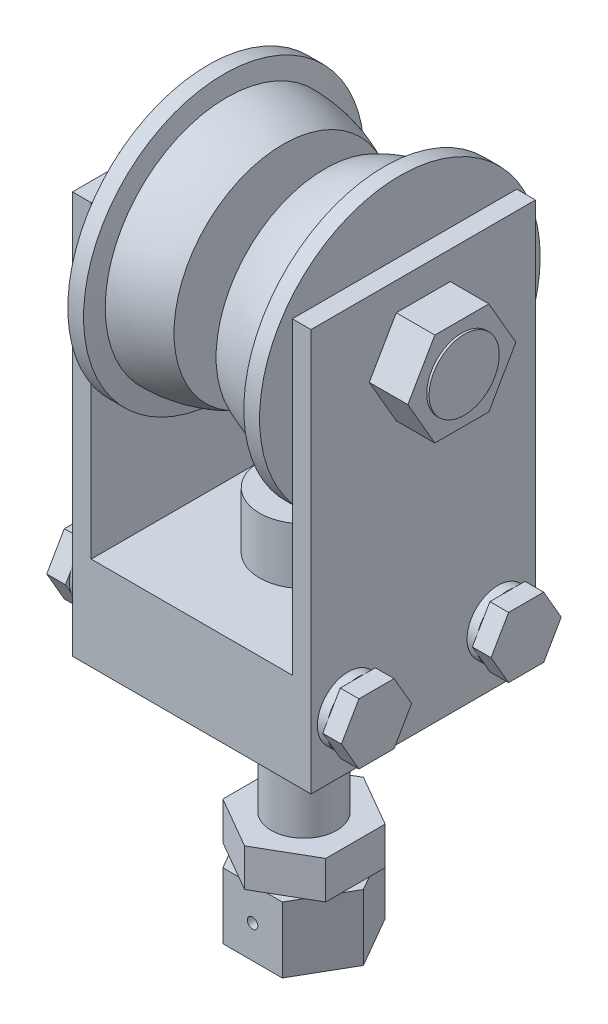
SolidWorks part; units mm, degrees
ref_plane "Front" through (0, 0, 0) normal (0, 0, 1) x (1, 0, 0)
ref_plane "Top" through (0, 0, 0) normal (0, 1, 0) x (1, 0, 0)
ref_plane "Right" through (0, 0, 0) normal (1, 0, 0) x (0, 0, -1)
ref_plane "Z PLANE" through (0, 0, 0) normal (0, 0, 1) x (1, 0, 0)
ref_plane "YOKE BOTTOM" through (0, 0, 0) normal (0, 1, 0) x (-1, 0, 0)
ref_plane "X PLANE" through (0, 0, 0) normal (1, 0, 0) x (0, 0, -1)
sketch "YOKE CROSS SECTION" plane through (0, 0, 0) normal (1, 0, 0) x (0, 0, -1)
  line L0 (0, 0) -> (0, 57.0916) construction
  line L1 (0, 84.8167) -> (0, -84.8167) construction
  line L2 (-76.2, 0) -> (76.2, 0)
  line L3 (69.1602, 0) -> (-69.1602, 0) construction
  line L4 (76.2, 0) -> (76.2, 63.5)
  line L5 (-76.2, 0) -> (-76.2, 63.5)
  line L6 (76.2, 63.5) -> (-76.2, 63.5)
  point P12 (0, 63.5)
  dimension "D1" = 63.5
  dimension "D2" = 152.4
ref_plane "1/2 YOKE LENGTH (A)" through (68.2625, 0, 0) normal (1, 0, 0) x (0, 0, -1)
extrude "YOKE" add sketch "YOKE CROSS SECTION" along normal up to surface (68.2625 mm away) up to plane "1/2 YOKE LENGTH (A)"
sketch "SIDEPLATE PROFILE" plane through (68.2625, 0, 0) normal (1, 0, 0) x (0, 0, -1)
  line L0 (0, 0) -> (0, 74.7424) construction
  line L1 (0, 84.8167) -> (0, -84.8167) construction
  line L2 (-76.2, 0) -> (76.2, 0)
  line L3 (76.2, 0) -> (76.2, 273.05)
  line L4 (-76.2, 0) -> (-76.2, 273.05)
  line L5 (76.2, 273.05) -> (-76.2, 273.05)
  point P11 (0, 273.05)
  dimension "D1" = 273.05
ref_plane "WHEEL HEIGHT" through (0, 222.25, 0) normal (0, 1, 0) x (-1, 0, 0)
ref_plane "SCREW LOCATION X" through (0, 0, 50.8) normal (0, 0, 1) x (1, 0, 0)
ref_plane "SCREW LOCATION Y" through (0, 38.1, 0) normal (0, 1, 0) x (-1, 0, 0)
extrude "SIDEPLATE" add sketch "SIDEPLATE PROFILE" along normal blind 12.7
sketch "WHEEL PIN NUT PROFILE" plane through (80.9625, 0, 0) normal (1, 0, 0) x (0, 0, -1)
  line L0 (0, 84.8167) -> (0, -84.8167) construction
  line L1 (36.6617, 222.25) -> (18.3309, 254)
  line L2 (18.3309, 254) -> (-18.3309, 254)
  line L3 (-18.3309, 254) -> (-36.6617, 222.25)
  line L4 (-36.6617, 222.25) -> (-18.3309, 190.5)
  line L5 (-18.3309, 190.5) -> (18.3309, 190.5)
  line L6 (18.3309, 190.5) -> (36.6617, 222.25)
  line L7 (69.1602, 222.25) -> (-69.1602, 222.25) construction
  circle A0 centre (0, 222.25) radius 31.75 construction
  dimension "D1" = 63.5
extrude "WHEEL PIN NUT" add sketch "WHEEL PIN NUT PROFILE" along normal blind 26.1937
sketch "WHEEL PIN PROJECTION PROFILE" plane through (107.1563, 0, 0) normal (1, 0, 0) x (0, 0, -1)
  line L0 (0, 84.8167) -> (0, -84.8167) construction
  line L1 (69.1602, 222.25) -> (-69.1602, 222.25) construction
  circle A0 centre (0, 222.25) radius 23.8125
  dimension "D1" = 47.625
extrude "WHEEL PIN PROJECTION" add sketch "WHEEL PIN PROJECTION PROFILE" along normal blind 1.5875
sketch "LOCKNUTS PROFILE" plane through (80.9625, 0, 0) normal (1, 0, 0) x (0, 0, -1)
  line L0 (-50.8, 84.8167) -> (-50.8, -84.8167) construction
  line L1 (50, 38.1) -> (-50, 38.1) construction
  circle A0 centre (-50.8, 38.1) radius 21.0947
  dimension "D1" = 42.1894
extrude "LOCKNUTS" add sketch "LOCKNUTS PROFILE" along normal blind 6.35
sketch "SCREWS PROFILE" plane through (87.3125, 0, 0) normal (1, 0, 0) x (0, 0, -1)
  line L0 (50, 38.1) -> (-50, 38.1) construction
  line L1 (-26.9699, 38.1) -> (-38.8849, 58.7375)
  line L2 (-38.8849, 58.7375) -> (-62.7151, 58.7375)
  line L3 (-62.7151, 58.7375) -> (-74.6301, 38.1)
  line L4 (-74.6301, 38.1) -> (-62.7151, 17.4625)
  line L5 (-62.7151, 17.4625) -> (-38.8849, 17.4625)
  line L6 (-38.8849, 17.4625) -> (-26.9699, 38.1)
  line L7 (-50.8, 84.8167) -> (-50.8, -84.8167) construction
  circle A0 centre (-50.8, 38.1) radius 20.6375 construction
  dimension "D1" = 41.275
extrude "SCREWS" add sketch "SCREWS PROFILE" along normal blind 12.7
sketch "PROFILE" plane through (0, 63.5, 0) normal (0, 1, 0) x (-1, 0, 0)
  line L0 (84.8167, 0) -> (-84.8167, 0) construction
  line L1 (0, 83.2389) -> (0, -83.2389) construction
  circle A0 centre (0, 0) radius 30.1625
  dimension "D1" = 60.325
extrude "KING BOLT HEAD" add sketch "PROFILE" along normal blind 38.1
mirror "Mirror1" about plane through (0, 0, 0) normal (0, 0, 1) of "SCREWS", "LOCKNUTS"
mirror "Mirror5" about plane through (0, 0, 0) normal (1, 0, 0) of bodies 112
ref_plane "TOP OF NUT" through (0, -88.9, 0) normal (0, 1, 0) x (-1, 0, 0)
sketch "DIA." plane through (0, 0, 0) normal (0, -1, 0) x (1, 0, 0)
  line L0 (84.8167, 0) -> (-84.8167, 0) construction
  line L1 (0, -83.2389) -> (0, 83.2389) construction
  circle A0 centre (0, 0) radius 22.225
  dimension "D1" = 44.45
extrude "KING BOLT" add sketch "DIA." along normal up to surface (88.9 mm away) up to plane "TOP OF NUT"
sketch "KING BOLT JAN NUT PROFILE" plane through (0, -88.9, 0) normal (0, -1, 0) x (1, 0, 0)
  line L0 (84.8167, 0) -> (-84.8167, 0) construction
  line L1 (0, -40.3279) -> (34.925, -20.164)
  line L2 (34.925, -20.164) -> (34.925, 20.164)
  line L3 (34.925, 20.164) -> (0, 40.3279)
  line L4 (0, 40.3279) -> (-34.925, 20.164)
  line L5 (-34.925, 20.164) -> (-34.925, -20.164)
  line L6 (-34.925, -20.164) -> (0, -40.3279)
  line L7 (0, -83.2389) -> (0, 83.2389) construction
  circle A0 centre (0, 0) radius 34.925 construction
  dimension "D1" = 69.85
extrude "KING BOLT JAM NUT" add sketch "KING BOLT JAN NUT PROFILE" along normal blind 25.6286
sketch "KING BOLT NUT PROFILE" plane through (0, -114.5286, 0) normal (0, -1, 0) x (1, 0, 0)
  line L1 (40.3279, 0) -> (20.164, 34.925)
  line L2 (20.164, 34.925) -> (-20.164, 34.925)
  line L3 (-20.164, 34.925) -> (-40.3279, 0)
  line L4 (-40.3279, 0) -> (-20.164, -34.925)
  line L5 (-20.164, -34.925) -> (20.164, -34.925)
  line L6 (20.164, -34.925) -> (40.3279, 0)
  line L10 (0, -83.2389) -> (0, 83.2389) construction
  line L11 (84.8167, 0) -> (-84.8167, 0) construction
  circle A0 centre (0, 0) radius 34.925 construction
  dimension "D1" = 69.85
extrude "KING BOLT NUT" add sketch "KING BOLT NUT PROFILE" along normal blind 44.6786
sketch "Sketch5" plane through (0, -159.2072, 0) normal (0, -1, 0) x (1, 0, 0)
  circle A0 centre (0, 0) radius 22.225 construction
  circle A1 centre (0, 0) radius 22.225
extrude "EXTENDED KING BOLT" add sketch "Sketch5" along normal blind 9.525
chamfer "Chamfer1" distance 2.3812 angle 45 1 edges at (0, -168.7322, -22.225)
ref_plane "MOUNTING REF PLANE" through (0, -34.925, 0) normal (0, 1, 0) x (-1, 0, 0)
sketch "Sketch6" plane through (0, 0, 0) normal (0, 0, 1) x (1, 0, 0)
  line L0 (68.2625, 254) -> (68.2625, 222.25)
  line L1 (68.2625, 222.25) -> (68.2625, 254)
  line L2 (14.2875, 222.25) -> (14.2875, 296.2219)
  line L3 (68.2625, 222.25) -> (14.2875, 222.25)
  line L4 (52.3875, 304.8) -> (54.399, 317.5)
  line L5 (65.0875, 254) -> (65.0875, 317.5)
  line L6 (65.0875, 254) -> (68.2625, 254)
  line L7 (54.399, 317.5) -> (65.0875, 317.5)
  line L8 (69.1602, 222.25) -> (-69.1602, 222.25) construction
  line L11 (68.2625, -75.0522) -> (68.2625, 75.0522) construction
  arc A0 (52.3875, 304.8) -> (14.2875, 296.2219) centre (52.3875, 215.9) ccw
  dimension "D7" = 88.9
  dimension "D1" = 31.75
  dimension "D2" = 63.5
  dimension "D3" = 53.975
  dimension "D4" = 73.9719
  dimension "D5" = 82.55
  dimension "D6" = 3.175
  dimension "D8" = 6.35
  dimension "D9" = 15.875
  dimension "D10" = 12.8583
revolve "WHEEL" add sketch "Sketch6" angle 360 about L3
mirror "Mirror6" about plane through (0, 0, 0) normal (1, 0, 0) of "WHEEL"
sketch "Sketch7" plane through (0, 0, 34.925) normal (0, 0, 1) x (1, 0, 0)
  line L0 (0, -83.2389) -> (0, 83.2389) construction
  line L1 (-20.164, -159.2072) -> (-40.3279, -159.2072) construction
  circle A0 centre (0, -136.9822) radius 3.5719
  dimension "D1" = 7.1437
  dimension "D2" = 22.225
extrude "COTTER PIN HOLE" cut sketch "Sketch7" against normal up to next
sketch "Sketch8" plane through (0, 0, 0) normal (0, -1, 0) x (1, 0, 0)
  circle A0 centre (0, 0) radius 25.4
  circle A1 centre (0, 0) radius 30.1625
  dimension "D1" = 50.8
  dimension "D2" = 60.325
extrude "SPACER" [suppressed] add sketch "Sketch8" along normal blind 12.7
ref_plane "TREAD OF TRACK" through (0, 139.7, 0) normal (0, 1, 0) x (-1, 0, 0)
